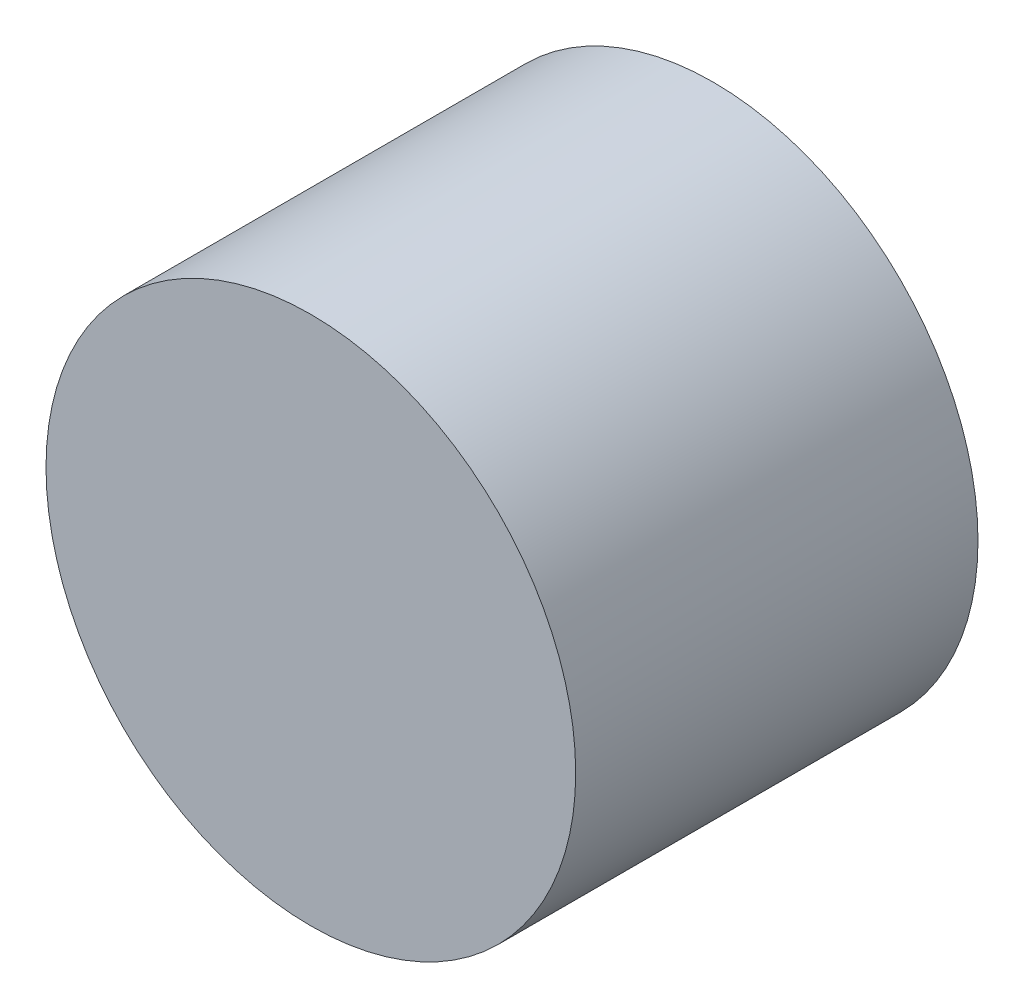
SolidWorks part; units mm, degrees
ref_plane "Front Plane" through (0, 0, 0) normal (0, 0, 1) x (1, 0, 0)
ref_plane "Top Plane" through (0, 0, 0) normal (0, 1, 0) x (1, 0, 0)
ref_plane "Right Plane" through (0, 0, 0) normal (1, 0, 0) x (0, 0, -1)
sketch "Sketch1" plane through (0, 0, 0) normal (0, 0, 1) x (1, 0, 0)
  circle A0 centre (0, 0) radius 5.5
  circle A1 centre (0, 0) radius 7.9
  dimension "D1" = 11
  dimension "D2" = 2.4
extrude "Boss-Extrude1" add sketch "Sketch1" along normal blind 2 contours A0 | A1 A0
sketch "Sketch2" plane through (0, 0, 0) normal (0, 0, -1) x (-1, 0, 0)
  circle A1 centre (0, 0) radius 7.9 construction
  circle A2 centre (0, 0) radius 5.5
  circle A3 centre (0, 0) radius 5.5
  circle A4 centre (0, 0) radius 7.9
  dimension "D1" = 2.4
extrude "Boss-Extrude2" add sketch "Sketch2" along normal blind 10
